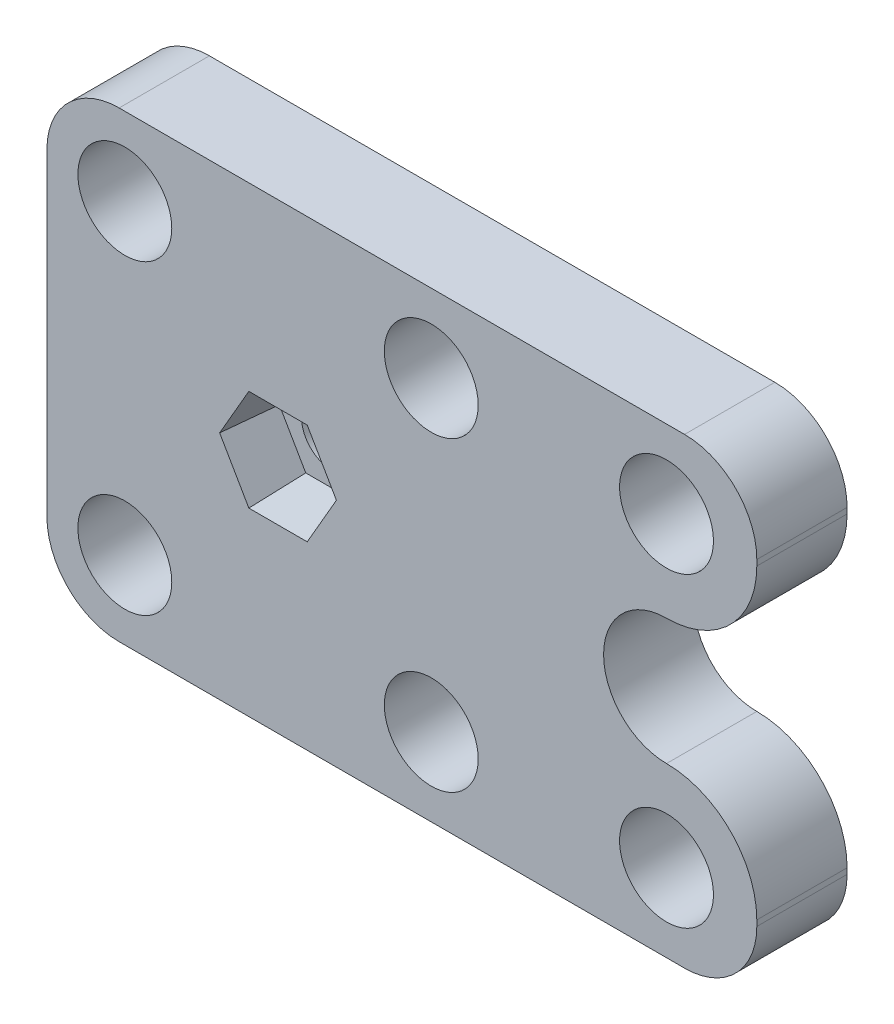
SolidWorks part; units mm, degrees
ref_plane "Plan de face" through (0, 0, 0) normal (0, 0, 1) x (1, 0, 0)
ref_plane "Plan de dessus" through (0, 0, 0) normal (0, 1, 0) x (1, 0, 0)
ref_plane "Plan de droite" through (0, 0, 0) normal (1, 0, 0) x (0, 0, -1)
sketch "Esquisse1" plane through (0, 0, 0) normal (0, 0, 1) x (1, 0, 0)
  line L0 (0, 0) -> (30, 0) construction
  line L1 (-12.8, -12.8) -> (12.8, -12.8)
  line L2 (-12.8, -12.8) -> (-12.8, 12.8)
  line L3 (-12.8, 12.8) -> (12.8, 12.8)
  line L5 (-12.8, -12.8) -> (12.8, 12.8) construction
  line L6 (-12.8, 12.8) -> (12.8, -12.8) construction
  line L7 (30, 0) -> (38.4853, 8.4853) construction
  line L8 (21.5147, 8.4853) -> (21.5147, -8.4853) construction
  line L9 (21.5147, -8.4853) -> (38.4853, -8.4853) construction
  line L10 (38.4853, -8.4853) -> (38.4853, 8.4853) construction
  line L11 (38.4853, 8.4853) -> (21.5147, 8.4853) construction
  line L12 (12.8, 12.8) -> (26.5147, 12.8)
  line L13 (26.5147, 12.8) -> (26.5147, 8.4853)
  line L14 (12.8, -12.8) -> (26.5147, -12.8)
  line L15 (26.5147, -12.8) -> (26.5147, -8.4853)
  circle A0 centre (0, 0) radius 1.7
  circle A1 centre (-8.4853, 8.4853) radius 2.6
  circle A2 centre (8.4853, 8.4853) radius 2.6
  circle A3 centre (8.4853, -8.4853) radius 2.6
  circle A4 centre (-8.4853, -8.4853) radius 2.6
  circle A5 centre (30, 0) radius 7.5 construction
  circle A6 centre (38.4853, 8.4853) radius 2.6 construction
  circle A7 centre (38.4853, -8.4853) radius 2.6 construction
  circle A8 centre (21.5147, -8.4853) radius 2.6
  circle A9 centre (21.5147, 8.4853) radius 2.6
  arc A10 (21.5147, 3.4853) -> (26.5147, 8.4853) centre (21.5147, 8.4853) ccw
  arc A11 (21.5147, -3.4853) -> (26.5147, -8.4853) centre (21.5147, -8.4853) cw
  arc A12 (21.5147, -3.4853) -> (21.5147, 3.4853) centre (21.5147, 0) cw
  point P0 (0, 0)
  point P19 (0, 0)
  point P30 (30, 0)
  dimension "D1" = 25.6
  dimension "D3" = 12
  dimension "D4" = 4
  dimension "D5" = 4
  dimension "D2" = 25.6
extrude "Boss.-Extru.1" add sketch "Esquisse1" along normal blind 5
sketch "Esquisse2" plane through (0, 0, 5) normal (0, 0, 1) x (1, 0, 0)
  line L1 (3.2332, 0) -> (1.6166, 2.8)
  line L2 (1.6166, 2.8) -> (-1.6166, 2.8)
  line L3 (-1.6166, 2.8) -> (-3.2332, 0)
  line L4 (-3.2332, 0) -> (-1.6166, -2.8)
  line L5 (-1.6166, -2.8) -> (1.6166, -2.8)
  line L6 (1.6166, -2.8) -> (3.2332, 0)
  circle A0 centre (0, 0) radius 2.8 construction
extrude "Enlèv. mat.-Extru.1" cut sketch "Esquisse2" against normal blind 3 draft 5
fillet "Congé1" radius 4 4 edges at (-12.8, -12.8, 2.5) (-12.8, 12.8, 2.5) (26.5147, -12.8, 2.5) (26.5147, 12.8, 2.5)
